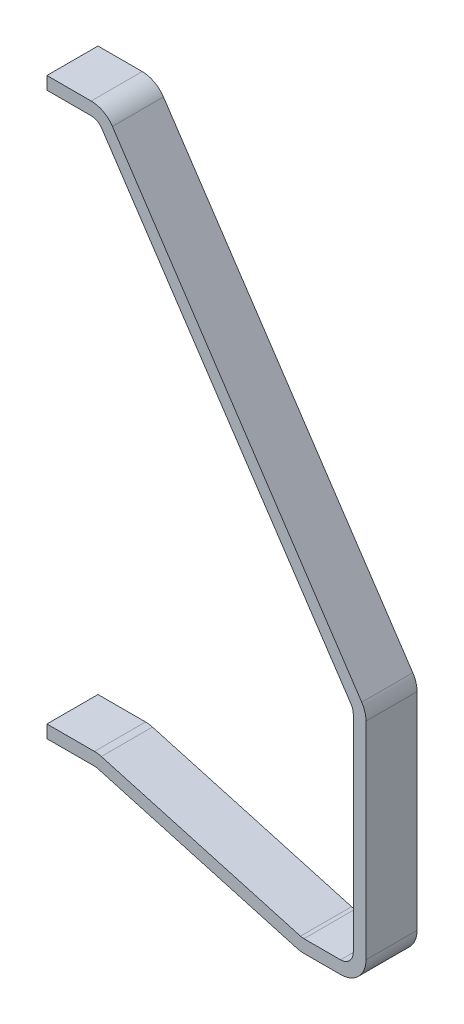
SolidWorks part; units mm, degrees
ref_plane "Front Plane" through (0, 0, 0) normal (0, 0, 1) x (1, 0, 0)
ref_plane "Top Plane" through (0, 0, 0) normal (0, 1, 0) x (1, 0, 0)
ref_plane "Right Plane" through (0, 0, 0) normal (1, 0, 0) x (0, 0, -1)
sketch "Sketch1" plane through (0, 0, 0) normal (0, 0, 1) x (1, 0, 0)
  line L0 (0, 0) -> (25.4, 0)
  line L1 (25.4, 0) -> (152.4, -190.5)
  line L2 (152.4, -190.5) -> (152.4, -301.625)
  line L3 (152.4, -301.625) -> (127, -301.625)
  line L4 (127, -301.625) -> (25.4, -273.05)
  line L5 (25.4, -273.05) -> (0, -273.05)
  dimension "D1" = 25.4
  dimension "D2" = 127
  dimension "D3" = 111.125
  dimension "D4" = 25.4
  dimension "D5" = 190.5
  dimension "D6" = 25.4
  dimension "D7" = 273.05
  dimension "D8" = 101.6
extrude "Extrude-Thin1" add sketch "Sketch1" along normal blind 25.4 thin thin type one direction reverse wall 6.35
fillet "Fillet1" radius 6.35 5 edges at (24.524, -279.4, 12.7) (127, -301.625, 12.7) (152.4, -301.625, 12.7) (152.4, -190.5, 12.7) (25.4, 0, 12.7)
fillet "Fillet2" radius 12.7 5 edges at (25.4, -273.05, 12.7) (126.124, -307.975, 12.7) (158.75, -307.975, 12.7) (158.75, -188.5774, 12.7) (28.7984, 6.35, 12.7)
